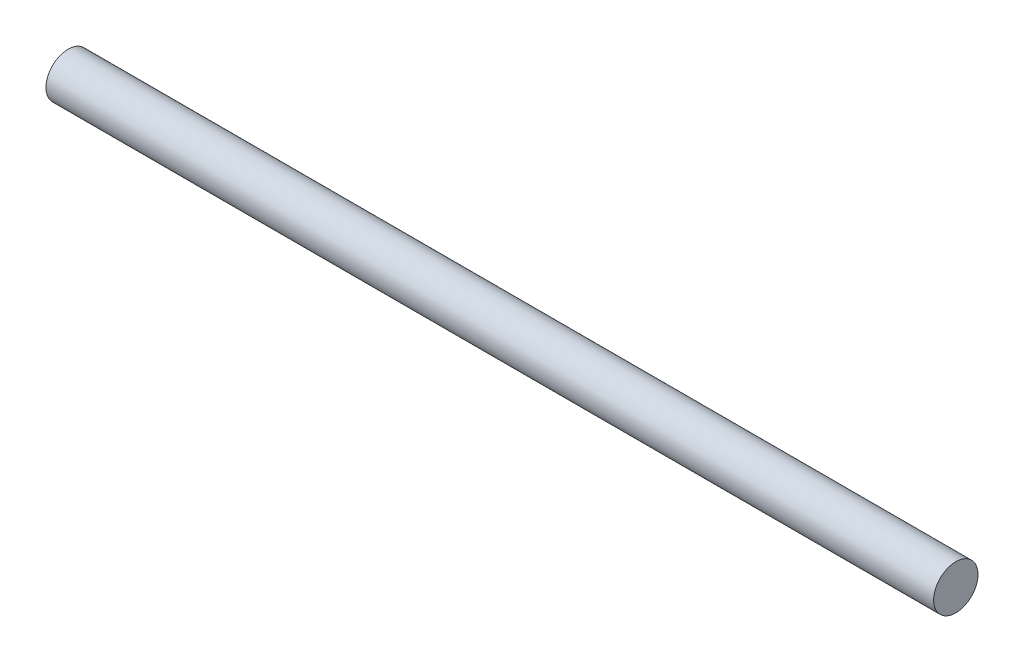
SolidWorks part; units mm, degrees
ref_plane "Front Plane" through (0, 0, 0) normal (0, 0, 1) x (1, 0, 0)
ref_plane "Top Plane" through (0, 0, 0) normal (0, 1, 0) x (1, 0, 0)
ref_plane "Right Plane" through (0, 0, 0) normal (1, 0, 0) x (0, 0, -1)
sketch "Sketch1" plane through (0, 0, 0) normal (1, 0, 0) x (0, 0, -1)
  circle A0 centre (-22.6945, 11.063) radius 0.75
  dimension "D1" = 1.5
extrude "Boss-Extrude1" add sketch "Sketch1" along normal blind 30
